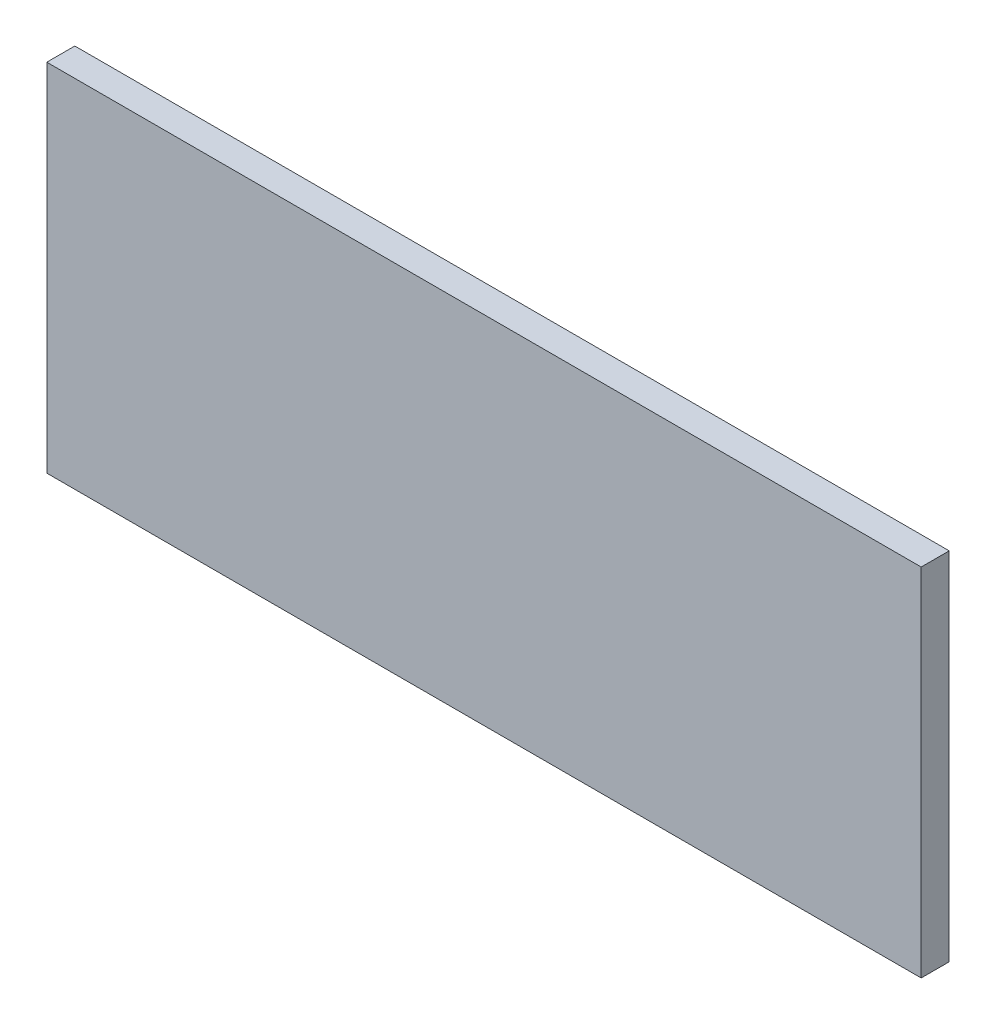
SolidWorks part; units mm, degrees
ref_plane "Front Plane" through (0, 0, 0) normal (0, 0, 1) x (1, 0, 0)
ref_plane "Top Plane" through (0, 0, 0) normal (0, 1, 0) x (1, 0, 0)
ref_plane "Right Plane" through (0, 0, 0) normal (1, 0, 0) x (0, 0, -1)
sketch "Sketch2" plane through (0, 0, 0) normal (0, 0, 1) x (1, 0, 0)
  line L1 (-355.7786, 50.7088) -> (-43.7786, 50.7088)
  line L2 (-355.7786, 50.7088) -> (-355.7786, -76.2912)
  line L3 (-355.7786, -76.2912) -> (-43.7786, -76.2912)
  line L4 (-43.7786, 50.7088) -> (-43.7786, -76.2912)
  dimension "D1" = 312
  dimension "D2" = 127
extrude "Boss-Extrude1" add sketch "Sketch2" along normal blind 10
